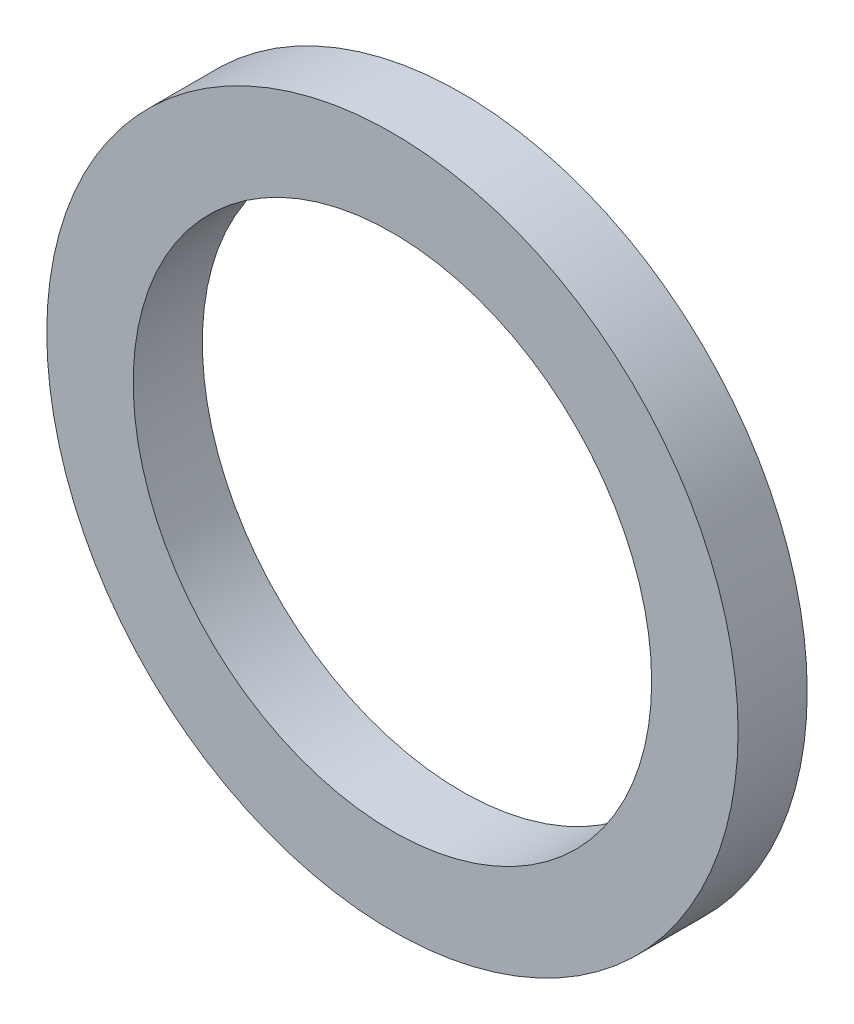
SolidWorks part; units mm, degrees
ref_plane "FRONT" through (0, 0, 0) normal (0, 0, 1) x (1, 0, 0)
ref_plane "TOP" through (0, 0, 0) normal (0, 1, 0) x (1, 0, 0)
ref_plane "SIDE" through (0, 0, 0) normal (1, 0, 0) x (0, 0, -1)
sketch "Sketch1" plane through (0, 0, 0) normal (0, 0, 1) x (1, 0, 0)
  circle A0 centre (0, 21.4613) radius 4.7625 construction
  circle A1 centre (0, 21.4613) radius 4.7625
  circle A2 centre (0, 21.4613) radius 6.35
  arc A3 (-3.7079, 26.6162) -> (3.7079, 26.6162) centre (0, 21.4613) ccw construction
extrude "Base-Extrude" add sketch "Sketch1" along normal blind 1.27
